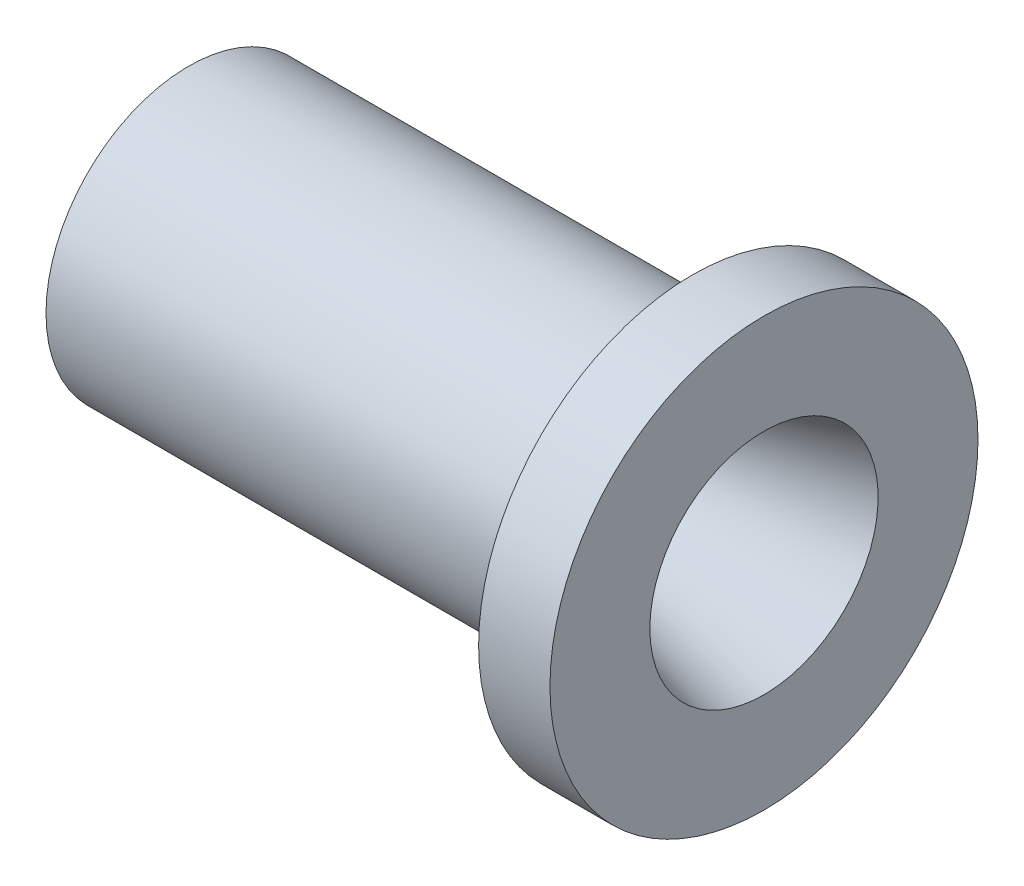
SolidWorks part; units mm, degrees
ref_plane "Front Plane" through (0, 0, 0) normal (0, 0, 1) x (1, 0, 0)
ref_plane "Top Plane" through (0, 0, 0) normal (0, 1, 0) x (1, 0, 0)
ref_plane "Right Plane" through (0, 0, 0) normal (1, 0, 0) x (0, 0, -1)
sketch "Sketch1" plane through (0, 0, 0) normal (0, 0, 1) x (1, 0, 0)
  line L0 (0, 0) -> (2773.6243, 0) construction
  line L1 (-16.7591, 5.08) -> (-6.5991, 5.08)
  line L2 (-6.5991, 5.08) -> (0, 1.27)
  line L3 (0, 1.27) -> (1.27, 1.27)
  line L4 (1.27, 1.27) -> (34.4479, 10.16)
  line L5 (34.4479, 10.16) -> (34.4479, 19.05)
  line L6 (34.4479, 19.05) -> (28.0979, 19.05)
  line L7 (28.0979, 19.05) -> (28.0979, 12.7)
  line L8 (28.0979, 12.7) -> (-16.7591, 12.7)
  line L9 (-16.7591, 12.7) -> (-16.7591, 5.08)
  line L10 (0, 0) -> (0, 50000) construction
  dimension "D1" = 1.27
  dimension "D2" = 1.27
  dimension "D3" = 5.08
  dimension "D4" = 30
  dimension "D5" = 15
  dimension "D8" = 10.16
  dimension "D9" = 10.16
  dimension "D10" = 6.35
  dimension "D6" = 12.7
  dimension "D7" = 19.05
revolve "Revolve1" add sketch "Sketch1" angle 360 about L0
equation "\"r_throat\"= 0.05"
equation "\"r_exit\"= 0.4"
equation "\"l_throat\"= 0.05"
equation "\"OD\"= 1"
equation "\"thread_nom_diam\"= 0.4"
equation "\"l_thread\"= 0.4"
equation "\"l_flange\" = 0.25"
equation "\"D9@Sketch1\"=\"l_thread\""
equation "\"D3@Sketch1\"=\"thread_nom_diam\"/2"
equation "\"D2@Sketch1\"=\"l_throat\""
equation "\"D1@Sketch1\"=\"r_throat\""
equation "\"D8@Sketch1\"=\"r_exit\""
equation "\"D10@Sketch1\"=\"l_flange\""
equation "\"d_flange\" = 1.5"
equation "\"D6@Sketch1\"=\"OD\"/2"
equation "\"D7@Sketch1\"=\"d_flange\"/2"
